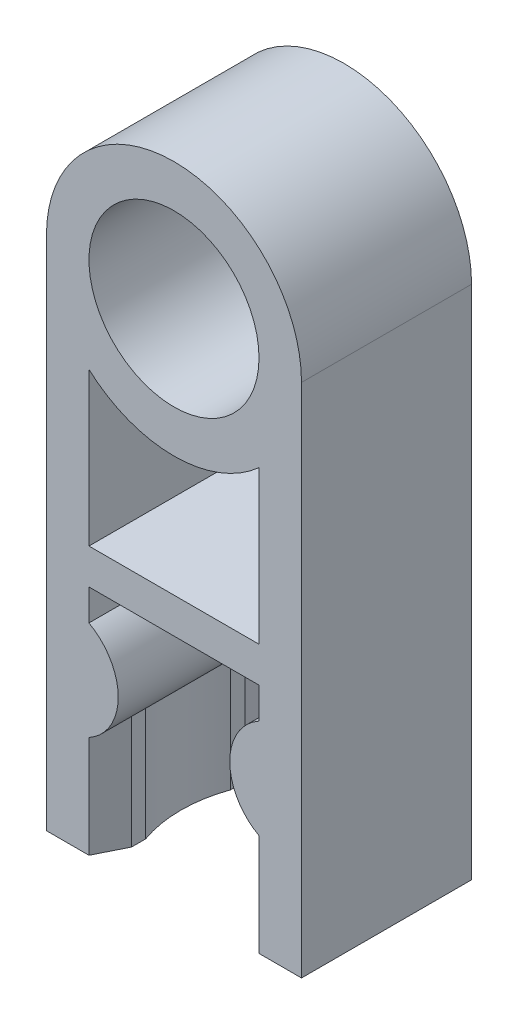
SolidWorks part; units mm, degrees
ref_plane "前视基准面" through (0, 0, 0) normal (0, 0, 1) x (1, 0, 0)
ref_plane "上视基准面" through (0, 0, 0) normal (0, 1, 0) x (1, 0, 0)
ref_plane "右视基准面" through (0, 0, 0) normal (1, 0, 0) x (0, 0, -1)
sketch "草图1" plane through (0, 0, 0) normal (0, 0, 1) x (1, 0, 0)
  line L0 (-4.5, 0) -> (-4.5, -18.2)
  line L1 (4.5, 0) -> (4.5, -18.2)
  line L2 (-4.5, -18.2) -> (-3, -18.2)
  line L3 (-3, -18.2) -> (-3, -14.6)
  line L4 (4.5, -18.2) -> (3, -18.2)
  line L5 (3, -18.2) -> (3, -14.6)
  line L6 (-3, -11.1) -> (-3, -10)
  line L7 (-3, -10) -> (3, -10)
  line L8 (3, -10) -> (3, -11.1)
  arc A0 (4.5, 0) -> (-4.5, 0) centre (0, 0) ccw
  arc A1 (-3, -11.1) -> (-3, -14.6) centre (-3.9682, -12.85) cw
  arc A2 (3, -11.1) -> (3, -14.6) centre (3.9682, -12.85) ccw
  point P1 (0, 4.5)
  dimension "D1" = 9
  dimension "D10" = 14.5
  dimension "D11" = 2
  dimension "D12" = 2
  dimension "D2" = 18.2
  dimension "D3" = 18.2
  dimension "D4" = 1.5
  dimension "D5" = 1.5
  dimension "D6" = 1.1
  dimension "D7" = 1.1
  dimension "D8" = 3.5
  dimension "D9" = 3.5
extrude "凸台-拉伸1" add sketch "草图1" along normal blind 6
sketch "草图2" plane through (0, 0, 0) normal (0, 0, 1) x (1, 0, 0)
  line L0 (-3, -8.75) -> (-3, -3.3541)
  line L1 (3, -8.75) -> (3, -3.3541)
  line L2 (-3, -8.75) -> (3, -8.75)
  line L3 (-3, -10) -> (3, -10) construction
  circle A0 centre (0, 0) radius 3
  arc A1 (-3, -3.3541) -> (3, -3.3541) centre (0, 0) ccw
  dimension "D1" = 6
  dimension "D2" = 9
  dimension "D3" = 1.25
extrude "切除-拉伸1" cut sketch "草图2" along normal through all
sketch "草图3" plane through (0, -18.2, 0) normal (0, -1, 0) x (1, 0, 0)
  line L0 (-3, 6) -> (-3, 0)
  line L1 (-3, 0) -> (-2.5, 1)
  line L2 (-2.5, 1) -> (-2.5, 1.5)
  line L3 (-3, 6) -> (-2.5, 5)
  line L4 (-2.5, 5) -> (-2.5, 4.5)
  line L5 (0, 0) -> (0, 6.4845) construction
  line L6 (3, 0) -> (2.5, 1)
  line L7 (2.5, 1) -> (2.5, 1.5)
  line L8 (2.5, 5) -> (2.5, 4.5)
  line L9 (3, 6) -> (2.5, 5)
  line L10 (3, 6) -> (3, 0)
  arc A0 (-2.5, 1.5) -> (-2.5, 4.5) centre (1.7426, 3) cw
  arc A1 (2.5, 1.5) -> (2.5, 4.5) centre (-1.7426, 3) ccw
  dimension "D7" = 4.5
  dimension "D1" = 0.5
  dimension "D2" = 0.5
  dimension "D3" = 0.5
  dimension "D4" = 0.5
  dimension "D5" = 1.5
  dimension "D6" = 1.5
extrude "凸台-拉伸2" add sketch "草图3" against normal up to next
